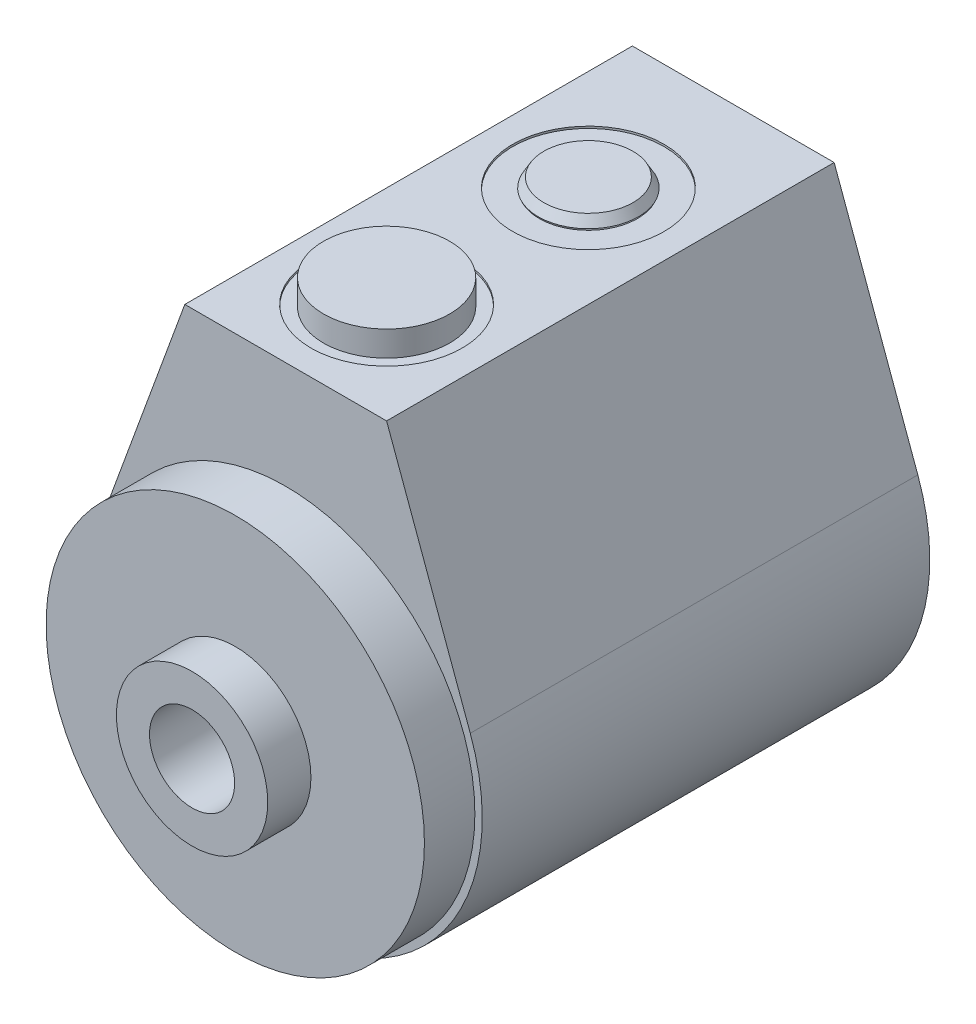
SolidWorks part; units mm, degrees
material "Alloy Steel"
ref_plane "Front Plane" through (0, 0, 0) normal (0, 0, 1) x (1, 0, 0)
ref_plane "Top Plane" through (0, 0, 0) normal (0, 1, 0) x (1, 0, 0)
ref_plane "Right Plane" through (0, 0, 0) normal (1, 0, 0) x (0, 0, -1)
ref_plane "Plane1" through (0, 0, 56.3372) normal (0, 0, 1) x (1, 0, 0)
sketch "Sketch1" plane through (0, 0, 56.3372) normal (0, 0, 1) x (1, 0, 0)
  line L0 (23.2331, 8.5012) -> (12.7, 37.2872)
  line L1 (12.7, 37.2872) -> (-12.7, 37.2872)
  line L2 (-12.7, 37.2872) -> (-23.2331, 8.5012)
  line L3 (0, 0) -> (0, 50.6803) construction
  arc A0 (-23.2331, 8.5012) -> (23.2331, 8.5012) centre (0, 0) ccw
  dimension "D1" = 49.4792
  dimension "D2" = 37.2872
  dimension "D3" = 12.7
extrude "Extrude1" add sketch "Sketch1" against normal blind 56.3372
hole_wizard "Hole1" positions "Sketch3" profile "Sketch2" legacy
sketch "Sketch3" plane through (0, 37.2872, 0) normal (0, 1, 0) x (-1, 0, 0)
  line L0 (-12.7, 56.3372) -> (12.7, 56.3372) construction
  point P0 (0, 43.6372)
  dimension "D1" = 12.7
sketch "Sketch2" plane through (0, 37.2872, 43.6372) normal (1, 0, 0) x (0, 0, 1)
  line L0 (0, 0) -> (0, 0.254)
  line L1 (0, 0.254) -> (9.525, 0.254)
  line L2 (9.525, 0.254) -> (9.525, 0)
  line L3 (9.525, 0) -> (0, 0)
  line L4 (0, 110) -> (0, -10) construction
  dimension "Diameter" = 19.05
  dimension "Depth" = 0.254
hole_wizard "Hole2" positions "Sketch5" profile "Sketch4" legacy
sketch "Sketch5" plane through (0, 0, 0) normal (0, 0, -1) x (-1, 0, 0)
  point P0 (0, 0)
sketch "Sketch4" plane through (0, 0, 0) normal (1, 0, 0) x (0, 1, 0)
  line L0 (0, 0) -> (0, 6.35)
  line L1 (0, 6.35) -> (11.938, 6.35)
  line L2 (11.938, 6.35) -> (11.938, 0)
  line L3 (11.938, 0) -> (0, 0)
  line L4 (0, 110) -> (0, -10) construction
  dimension "Diameter" = 23.876
  dimension "Depth" = 6.35
ref_plane "Plane2" through (0, 0, 0) normal (0, -1, 0) x (1, 0, 0)
sketch "Sketch7" plane through (0, 0, 0) normal (0, -1, 0) x (1, 0, 0)
  line L0 (9.525, 68.1228) -> (0, 68.1228)
  line L1 (0, 68.1228) -> (0, 56.3372)
  line L2 (0, 56.3372) -> (23.8125, 56.3372)
  line L3 (23.8125, 56.3372) -> (23.8125, 62.6872)
  line L4 (23.8125, 62.6872) -> (9.525, 62.6872)
  line L5 (9.525, 62.6872) -> (9.525, 68.1228)
  line L6 (0, 0) -> (0, 59.8975) construction
  line L7 (24.7396, 56.3372) -> (-24.7396, 56.3372) construction
  line L8 (-24.7396, 0) -> (24.7396, 0) construction
  dimension "D1" = 19.05
  dimension "D2" = 47.625
  dimension "D3" = 6.35
  dimension "D4" = 68.1228
revolve "Revolve2" add sketch "Sketch7" angle 360 about L6
sketch "Sketch6" plane through (0, 0, 0) normal (0, -1, 0) x (1, 0, 0)
  line L0 (9.525, 6.35) -> (0, 6.35)
  line L1 (0, 6.35) -> (0, 5.4102)
  line L2 (0, 5.4102) -> (9.525, 5.4102)
  line L3 (9.525, 5.4102) -> (9.525, 6.35)
  line L4 (-11.938, 6.35) -> (11.938, 6.35) construction
  line L5 (9.525, 68.1228) -> (-9.525, 68.1228) construction
  line L6 (0, 0) -> (0, 20.5953) construction
  dimension "D1" = 62.7126
  dimension "D2" = 19.05
revolve "Revolve1" add sketch "Sketch6" angle 360 about L6
sketch "Sketch8" plane through (0, 0, 32.639) normal (1, 0, 0) x (0, 0, -1)
  line L0 (-18.9357, 37.0332) -> (-10.9982, 37.0332)
  line L1 (-10.9982, 37.0332) -> (-10.9982, 40.2082)
  line L2 (-10.9982, 40.2082) -> (-18.9357, 40.2082)
  line L3 (-18.9357, 40.2082) -> (-18.9357, 37.0332)
  line L4 (-10.9982, 0) -> (-10.9982, 43.9417) construction
  line L5 (-1.4732, 37.0332) -> (-20.5232, 37.0332) construction
  line L7 (-20.5232, 37.2872) -> (-20.5232, 37.0332) construction
  line L8 (-1.4732, 37.0332) -> (-1.4732, 37.2872) construction
  dimension "D1" = 3.175
  dimension "D2" = 15.875
revolve "Revolve3" add sketch "Sketch8" angle 360 about L4
ref_plane "Plane4" through (0, 0, 18.2372) normal (0, 0, 1) x (1, 0, 0)
sketch "Sketch9" plane through (0, 0, 18.2372) normal (0, 0, 1) x (1, 0, 0)
  line L0 (-4.9784, 16.4592) -> (0, 16.4592)
  line L1 (0, 16.4592) -> (0, 37.2872)
  line L2 (0, 37.2872) -> (-9.525, 37.2872)
  line L3 (-9.525, 37.2872) -> (-9.525, 37.0332)
  line L4 (-9.525, 37.0332) -> (-6.1849, 37.0332)
  line L5 (-6.1849, 37.0332) -> (-5.6423, 34.4805)
  line L6 (-5.6423, 34.4805) -> (-4.9784, 33.8166)
  line L7 (-4.9784, 33.8166) -> (-4.9784, 16.4592)
  line L8 (0, 37.2872) -> (0, 0) construction
  line L9 (12.7, 37.2872) -> (-12.7, 37.2872) construction
  dimension "D1" = 0.254
  dimension "D2" = 20.828
  dimension "D3" = 9.9568
  dimension "D4" = 19.05
  dimension "D5" = 12
  dimension "D6" = 12.3698
  dimension "D7" = 45
  dimension "D8" = 2.5527
revolve "Cut-Revolve1" cut sketch "Sketch9" angle 360 about L8
ref_plane "Plane5" through (0, 0, 43.6372) normal (0, 0, 1) x (1, 0, 0)
sketch "Sketch10" plane through (0, 0, 43.6372) normal (0, 0, 1) x (1, 0, 0)
  line L0 (6.1849, 37.0332) -> (0, 37.0332)
  line L1 (0, 37.0332) -> (0, 23.5712)
  line L2 (0, 23.5712) -> (4.9784, 23.5712)
  line L3 (4.9784, 23.5712) -> (4.9784, 33.8166)
  line L4 (4.9784, 33.8166) -> (5.6423, 34.4805)
  line L5 (5.6423, 34.4805) -> (6.1849, 37.0332)
  line L6 (0, 0) -> (0, 56.4866) construction
  line L7 (9.525, 37.0332) -> (-9.525, 37.0332) construction
  dimension "D1" = 9.9568
  dimension "D2" = 13.462
  dimension "D3" = 45
  dimension "D4" = 12
  dimension "D5" = 12.3698
  dimension "D6" = 2.5527
revolve "Cut-Revolve2" cut sketch "Sketch10" angle 360 about L6
hole_wizard "Hole3" positions "Sketch12" profile "Sketch11" legacy
sketch "Sketch12" plane through (0, 0, 0) normal (0, 0, -1) x (-1, 0, 0)
  line L0 (0, 0) -> (0, -24.5872) construction
  point P0 (-18.2626, 0)
  dimension "D1" = 18.2626
sketch "Sketch11" plane through (18.2626, 0, 0) normal (1, 0, 0) x (0, 1, 0)
  line L0 (0, 0) -> (0, 12.7)
  line L1 (0, 12.7) -> (3.3147, 12.7)
  line L2 (3.3147, 12.7) -> (3.3147, 0)
  line L3 (3.3147, 0) -> (0, 0)
  line L4 (0, 110) -> (0, -10) construction
  dimension "Diameter" = 6.6294
  dimension "Depth" = 12.7
pattern_circular "CirPattern1" count 2 over 360 about axis through (0, 0, 0) along (0, 0, 1) of "Hole3"
hole_wizard "Hole5" positions "Sketch16" profile "Sketch15" legacy
sketch "Sketch16" plane through (0, 0, 5.4102) normal (0, 0, -1) x (-1, 0, 0)
  point P0 (0, 0)
sketch "Sketch15" plane through (0, 0, 5.4102) normal (1, 0, 0) x (0, 1, 0)
  line L0 (0, 0) -> (0, 62.7126)
  line L1 (0, 62.7126) -> (5.3594, 62.7126)
  line L2 (5.3594, 62.7126) -> (5.3594, 48.5838)
  line L3 (5.3594, 48.5838) -> (6.7437, 47.752)
  line L4 (6.7437, 47.752) -> (6.7437, 0)
  line L5 (6.7437, 0) -> (0, 0)
  line L6 (0, -6.13) -> (0, 109.2824) construction
  line L7 (-5.3594, 48.5838) -> (-6.7437, 47.752) construction
  line L8 (0, 62.7126) -> (-5.3594, 62.7126) construction
  dimension "Diameter" = 10.7188
  dimension "Depth" = 62.7126
  dimension "C-Drill Diameter" = 13.4874
  dimension "C-Drill Depth" = 47.752
  dimension "C-Drill Angle" = 118
sketch "Sketch17" plane through (0, 0, 0) normal (0, 0, -1) x (-1, 0, 0)
  circle A0 centre (0, 22.225) radius 5.6007
  dimension "D1" = 11.2014
  dimension "D2" = 22.225
extrude "Cut-Extrude1" cut sketch "Sketch17" against normal blind 1.3208
sketch "Sketch18" plane through (0, 0, 1.3208) normal (0, 0, -1) x (-1, 0, 0)
  circle A0 centre (0, 22.225) radius 2.5273
  dimension "D1" = 5.0546
extrude "Cut-Extrude2" cut sketch "Sketch18" against normal blind 12.7
sketch "Sketch19" plane through (0, 0, 0) normal (1, 0, 0) x (0, 0, -1)
  line L0 (-1.3208, 39.3281) -> (-1.3208, -29.7965) construction
  line L1 (0, 8.5012) -> (0, 37.2872) construction
  line L2 (-13.2588, 22.225) -> (-1.3208, 22.225) construction
  circle A0 centre (-0.4318, 26.9367) radius 0.889
  dimension "D2" = 1.778
  dimension "D1" = 1.3208
  dimension "D3" = 4.7117
revolve "Revolve4" add sketch "Sketch19" angle 360 about axis through (0, 22.225, 14.0208) along (0, 0, -1)
sketch "Sketch20" plane through (0, 0, 0) normal (1, 0, 0) x (0, 0, -1)
  line L0 (-18.2372, 41.0544) -> (-18.2372, 27.524) construction
  line L1 (0, 8.5012) -> (0, 37.2872) construction
  line L2 (-18.2372, 38.481) -> (-12.6272, 38.481)
  line L3 (-12.6272, 38.481) -> (-11.938, 37.2872)
  line L4 (0, 37.2872) -> (-56.3372, 37.2872) construction
  line L5 (-11.938, 37.2872) -> (-18.2372, 37.2872)
  line L6 (-18.2372, 38.481) -> (-18.2372, 37.2872)
  dimension "D1" = 18.2372
  dimension "D2" = 6.2992
  dimension "D3" = 1.1938
  dimension "D4" = 60
revolve "Revolve5" add sketch "Sketch20" angle 360 about L0
